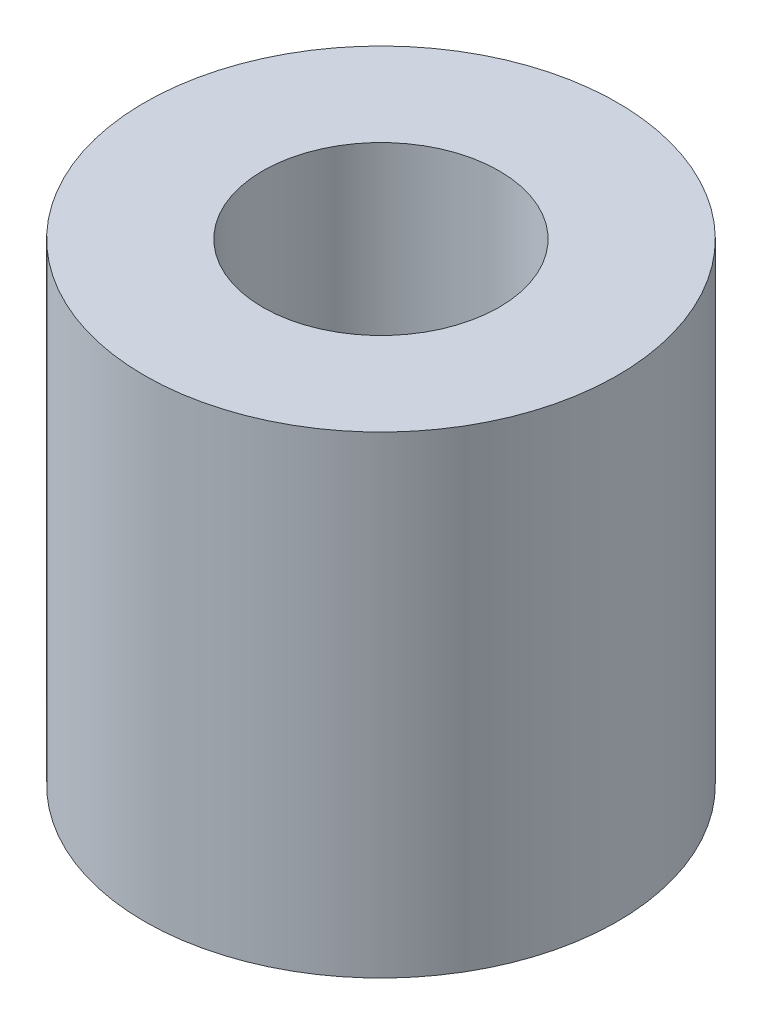
SolidWorks part; units mm, degrees
ref_plane "Face" through (0, 0, 0) normal (0, 0, 1) x (1, 0, 0)
ref_plane "Dessus" through (0, 0, 0) normal (0, 1, 0) x (1, 0, 0)
ref_plane "Droite" through (0, 0, 0) normal (1, 0, 0) x (0, 0, -1)
sketch "Esquisse1" plane through (0, 0, 0) normal (0, 1, 0) x (1, 0, 0)
  circle A0 centre (0, 0) radius 10
  circle A1 centre (0, 0) radius 5
  dimension "D1" = 20
  dimension "D2" = 10
extrude "Extrusion1" add sketch "Esquisse1" along normal blind 20
